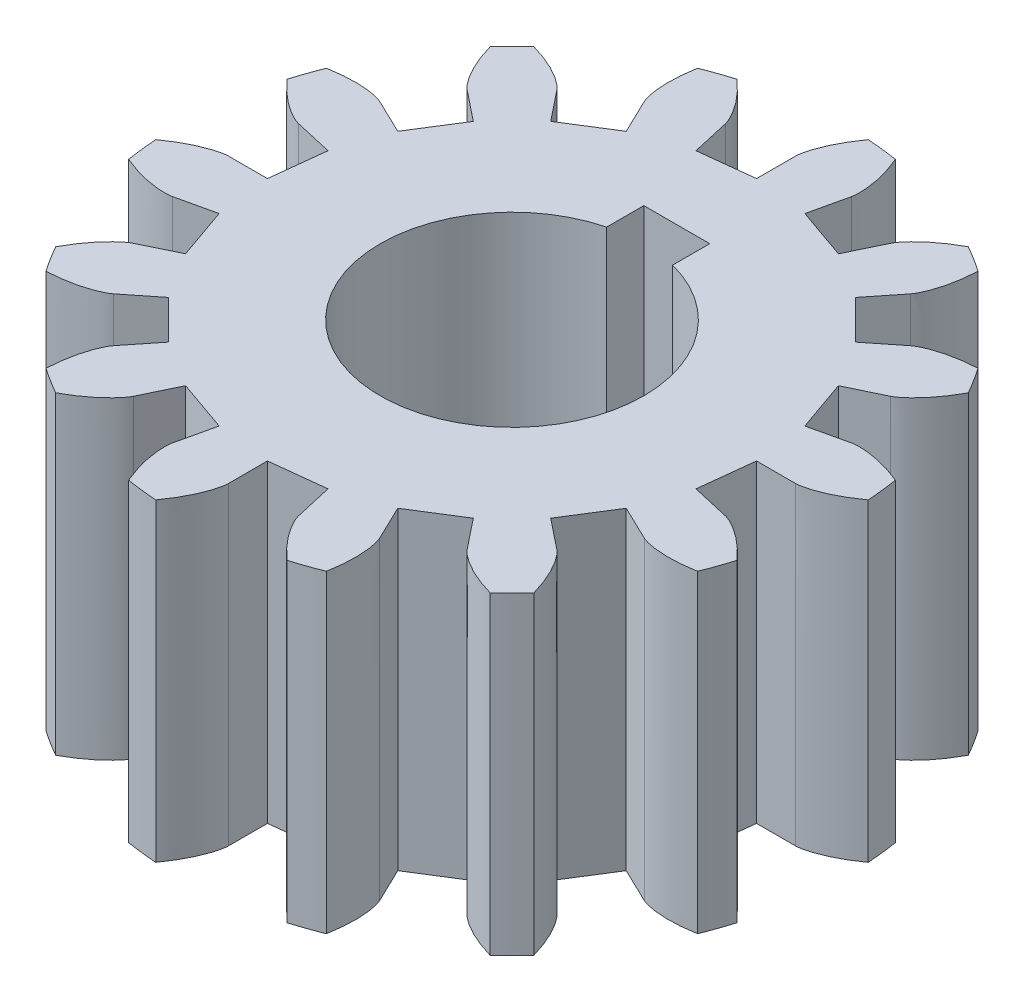
SolidWorks part; units mm, degrees
ref_plane "Front Plane" through (0, 0, 0) normal (0, 0, 1) x (1, 0, 0)
ref_plane "Top Plane" through (0, 0, 0) normal (0, 1, 0) x (1, 0, 0)
ref_plane "Right Plane" through (0, 0, 0) normal (1, 0, 0) x (0, 0, -1)
sketch "Sketch1" plane through (0, 0, 0) normal (0, 1, 0) x (1, 0, 0)
  line L0 (-8.6068, 0.0004) -> (-7.4206, 0.0003)
  line L1 (-7.7543, 3.7347) -> (-6.6856, 3.22)
  line L2 (-8.3911, -1.9148) -> (-7.2346, -1.6509)
  line L3 (-8.391, 1.9156) -> (-7.2345, 1.6515)
  line L4 (-5.366, 6.7293) -> (-4.6264, 5.8019)
  line L5 (-6.7289, 5.3666) -> (-5.8015, 4.6269)
  line L6 (-1.9148, 8.3911) -> (-1.6509, 7.2346)
  line L7 (-3.734, 7.7546) -> (-3.2194, 6.6859)
  line L8 (1.9156, 8.391) -> (1.6515, 7.2345)
  line L9 (0.0004, 8.6068) -> (0.0003, 7.4206)
  line L10 (5.3666, 6.7289) -> (4.6269, 5.8015)
  line L11 (3.7347, 7.7543) -> (3.22, 6.6856)
  line L12 (7.7546, 3.734) -> (6.6859, 3.2194)
  line L13 (6.7293, 5.366) -> (5.8019, 4.6264)
  line L14 (8.6068, -0.0004) -> (7.4206, -0.0003)
  line L15 (8.3911, 1.9148) -> (7.2346, 1.6509)
  line L16 (7.7543, -3.7347) -> (6.6856, -3.22)
  line L17 (8.391, -1.9156) -> (7.2345, -1.6515)
  line L18 (5.366, -6.7293) -> (4.6264, -5.8019)
  line L19 (6.7289, -5.3666) -> (5.8015, -4.6269)
  line L20 (1.9148, -8.3911) -> (1.6509, -7.2346)
  line L21 (3.734, -7.7546) -> (3.2194, -6.6859)
  line L22 (-1.9156, -8.391) -> (-1.6515, -7.2345)
  line L23 (-0.0004, -8.6068) -> (-0.0003, -7.4206)
  line L24 (-5.3666, -6.7289) -> (-4.6269, -5.8015)
  line L25 (-3.7347, -7.7543) -> (-3.22, -6.6856)
  line L26 (-7.7546, -3.734) -> (-6.6859, -3.2194)
  line L27 (-6.7293, -5.366) -> (-5.8019, -4.6264)
  line L28 (-7.2345, 1.6515) -> (-7.4206, 0.0003)
  line L29 (-5.8015, 4.6269) -> (-6.6856, 3.22)
  line L30 (-3.2194, 6.6859) -> (-4.6264, 5.8019)
  line L31 (0.0003, 7.4206) -> (-1.6509, 7.2346)
  line L33 (3.22, 6.6856) -> (1.6515, 7.2345)
  line L34 (5.8019, 4.6264) -> (4.6269, 5.8015)
  line L35 (7.2346, 1.6509) -> (6.6859, 3.2194)
  line L36 (7.2345, -1.6515) -> (7.4206, -0.0003)
  line L37 (5.8015, -4.6269) -> (6.6856, -3.22)
  line L38 (3.2194, -6.6859) -> (4.6264, -5.8019)
  line L39 (-0.0003, -7.4206) -> (1.6509, -7.2346)
  line L40 (-3.22, -6.6856) -> (-1.6515, -7.2345)
  line L41 (-5.8019, -4.6264) -> (-4.6269, -5.8015)
  line L42 (-7.2346, -1.6509) -> (-6.6859, -3.2194)
  line L44 (-1, 5) -> (1, 5)
  line L45 (-1, 5) -> (-1, 3.873)
  line L47 (1, 5) -> (1, 3.873)
  line L48 (1, 3) -> (1.008, 3.1002)
  arc A0 (-10.1378, -0.6707) -> (-10.033, -1.6011) centre (0, 0) ccw
  arc A1 (-9.4249, 3.7943) -> (-9.7342, 2.9106) centre (0, 0) ccw
  arc A2 (-6.8452, 7.5079) -> (-7.5073, 6.8459) centre (0, 0) ccw
  arc A3 (-2.9098, 9.7344) -> (-3.7935, 9.4252) centre (0, 0) ccw
  arc A4 (1.602, 10.0329) -> (0.6716, 10.1378) centre (0, 0) ccw
  arc A5 (5.7964, 8.3443) -> (5.0037, 8.8424) centre (0, 0) ccw
  arc A6 (8.8429, 5.0029) -> (8.3448, 5.7957) centre (0, 0) ccw
  arc A7 (10.1378, 0.6707) -> (10.033, 1.6011) centre (0, 0) ccw
  arc A8 (9.4249, -3.7943) -> (9.7342, -2.9106) centre (0, 0) ccw
  arc A9 (6.8452, -7.5079) -> (7.5073, -6.8459) centre (0, 0) ccw
  arc A10 (2.9098, -9.7344) -> (3.7935, -9.4252) centre (0, 0) ccw
  arc A11 (-1.602, -10.0329) -> (-0.6716, -10.1378) centre (0, 0) ccw
  arc A12 (-5.7964, -8.3443) -> (-5.0037, -8.8424) centre (0, 0) ccw
  arc A13 (-8.8429, -5.0029) -> (-8.3448, -5.7957) centre (0, 0) ccw
  arc A14 (-1, 3.873) -> (1, 3.873) centre (0, 0) ccw
  spline S0 degree 3 poles (-10.1378, -0.6707) (-10.0991, -0.6428) (-9.9923, -0.5669) (-9.8194, -0.4562) (-9.6238, -0.3435) (-9.442, -0.2507) (-9.2754, -0.1759) (-9.1252, -0.1174) (-8.9927, -0.0733) (-8.8788, -0.0417) (-8.7844, -0.0205) (-8.7103, -0.0081) (-8.6534, -0.0009) (-8.6212, 0) (-8.6068, 0.0004) knots 0.068878 0.068878 0.068878 0.068878 0.148295 0.284329 0.408535 0.520912 0.621459 0.710178 0.787068 0.852129 0.905361 0.946764 0.976338 1 1 1 1
  spline S1 degree 3 poles (-10.033, -1.6011) (-9.9891, -1.6198) (-9.8681, -1.6699) (-9.6748, -1.7394) (-9.4591, -1.8058) (-9.2612, -1.8558) (-9.0821, -1.8917) (-8.9227, -1.9153) (-8.7837, -1.9289) (-8.6656, -1.9343) (-8.5689, -1.934) (-8.4939, -1.9296) (-8.4368, -1.924) (-8.4052, -1.9177) (-8.3911, -1.9148) knots 0.068878 0.068878 0.068878 0.068878 0.148295 0.284329 0.408535 0.520912 0.621459 0.710178 0.787068 0.852129 0.905361 0.946764 0.976338 1 1 1 1
  spline S2 degree 3 poles (-9.4249, 3.7943) (-9.3779, 3.8027) (-9.2488, 3.8247) (-9.0449, 3.8494) (-8.8198, 3.8661) (-8.6157, 3.8708) (-8.4331, 3.8659) (-8.2725, 3.8535) (-8.1339, 3.8357) (-8.0176, 3.8148) (-7.9234, 3.7929) (-7.8512, 3.772) (-7.7968, 3.7538) (-7.7674, 3.7406) (-7.7543, 3.7347) knots 0.068878 0.068878 0.068878 0.068878 0.148295 0.284329 0.408535 0.520912 0.621459 0.710178 0.787068 0.852129 0.905361 0.946764 0.976338 1 1 1 1
  spline S3 degree 3 poles (-9.7342, 2.9106) (-9.7026, 2.8747) (-9.6154, 2.777) (-9.4714, 2.6306) (-9.3059, 2.4772) (-9.1493, 2.3462) (-9.0035, 2.2362) (-8.8701, 2.1458) (-8.7507, 2.0733) (-8.6467, 2.0171) (-8.5595, 1.9754) (-8.4899, 1.9468) (-8.4361, 1.9271) (-8.4048, 1.9191) (-8.391, 1.9156) knots 0.068878 0.068878 0.068878 0.068878 0.148295 0.284329 0.408535 0.520912 0.621459 0.710178 0.787068 0.852129 0.905361 0.946764 0.976338 1 1 1 1
  spline S4 degree 3 poles (-6.8452, 7.5079) (-6.7992, 7.4951) (-6.6734, 7.4588) (-6.4789, 7.3927) (-6.2689, 7.31) (-6.083, 7.2257) (-5.9206, 7.1421) (-5.7813, 7.0612) (-5.6641, 6.9851) (-5.5684, 6.9157) (-5.493, 6.8551) (-5.4371, 6.8049) (-5.396, 6.7649) (-5.3752, 6.7403) (-5.366, 6.7293) knots 0.068878 0.068878 0.068878 0.068878 0.148295 0.284329 0.408535 0.520912 0.621459 0.710178 0.787068 0.852129 0.905361 0.946764 0.976338 1 1 1 1
  spline S5 degree 3 poles (-7.5073, 6.8459) (-7.4945, 6.7999) (-7.4583, 6.674) (-7.3921, 6.4796) (-7.3095, 6.2695) (-7.2252, 6.0836) (-7.1416, 5.9212) (-7.0607, 5.7819) (-6.9846, 5.6647) (-6.9152, 5.569) (-6.8547, 5.4936) (-6.8045, 5.4377) (-6.7645, 5.3966) (-6.7398, 5.3758) (-6.7289, 5.3666) knots 0.068878 0.068878 0.068878 0.068878 0.148295 0.284329 0.408535 0.520912 0.621459 0.710178 0.787068 0.852129 0.905361 0.946764 0.976338 1 1 1 1
  spline S6 degree 3 poles (-2.9098, 9.7344) (-2.8739, 9.7029) (-2.7762, 9.6156) (-2.6298, 9.4717) (-2.4764, 9.3061) (-2.3455, 9.1495) (-2.2355, 9.0037) (-2.145, 8.8703) (-2.0725, 8.7509) (-2.0164, 8.6469) (-1.9747, 8.5596) (-1.9461, 8.4901) (-1.9264, 8.4362) (-1.9184, 8.405) (-1.9148, 8.3911) knots 0.068878 0.068878 0.068878 0.068878 0.148295 0.284329 0.408535 0.520912 0.621459 0.710178 0.787068 0.852129 0.905361 0.946764 0.976338 1 1 1 1
  spline S7 degree 3 poles (-3.7935, 9.4252) (-3.8019, 9.3782) (-3.8239, 9.2491) (-3.8487, 9.0452) (-3.8654, 8.8201) (-3.8701, 8.6161) (-3.8652, 8.4335) (-3.8528, 8.2728) (-3.8351, 8.1342) (-3.8141, 8.0179) (-3.7923, 7.9237) (-3.7713, 7.8515) (-3.7531, 7.7971) (-3.7399, 7.7677) (-3.734, 7.7546) knots 0.068878 0.068878 0.068878 0.068878 0.148295 0.284329 0.408535 0.520912 0.621459 0.710178 0.787068 0.852129 0.905361 0.946764 0.976338 1 1 1 1
  spline S8 degree 3 poles (1.602, 10.0329) (1.6206, 9.9889) (1.6708, 9.8679) (1.7403, 9.6747) (1.8066, 9.459) (1.8566, 9.2611) (1.8924, 9.082) (1.9161, 8.9225) (1.9296, 8.7835) (1.9351, 8.6655) (1.9347, 8.5688) (1.9303, 8.4937) (1.9247, 8.4366) (1.9184, 8.405) (1.9156, 8.391) knots 0.068878 0.068878 0.068878 0.068878 0.148295 0.284329 0.408535 0.520912 0.621459 0.710178 0.787068 0.852129 0.905361 0.946764 0.976338 1 1 1 1
  spline S9 degree 3 poles (0.6716, 10.1378) (0.6436, 10.0991) (0.5678, 9.9923) (0.457, 9.8193) (0.3443, 9.6238) (0.2515, 9.442) (0.1767, 9.2753) (0.1182, 9.1252) (0.0741, 8.9927) (0.0425, 8.8788) (0.0213, 8.7844) (0.0088, 8.7103) (0.0016, 8.6534) (0.0007, 8.6212) (0.0004, 8.6068) knots 0.068878 0.068878 0.068878 0.068878 0.148295 0.284329 0.408535 0.520912 0.621459 0.710178 0.787068 0.852129 0.905361 0.946764 0.976338 1 1 1 1
  spline S10 degree 3 poles (5.7964, 8.3443) (5.7942, 8.2966) (5.7869, 8.1658) (5.7656, 7.9615) (5.7318, 7.7384) (5.691, 7.5384) (5.6455, 7.3615) (5.5977, 7.2076) (5.5495, 7.0765) (5.5032, 6.9677) (5.461, 6.8807) (5.4245, 6.815) (5.3946, 6.766) (5.3752, 6.7403) (5.3666, 6.7289) knots 0.068878 0.068878 0.068878 0.068878 0.148295 0.284329 0.408535 0.520912 0.621459 0.710178 0.787068 0.852129 0.905361 0.946764 0.976338 1 1 1 1
  spline S11 degree 3 poles (5.0037, 8.8424) (4.9617, 8.8197) (4.847, 8.7564) (4.6722, 8.6486) (4.4858, 8.5213) (4.3233, 8.3978) (4.1836, 8.2801) (4.0657, 8.1702) (3.9685, 8.07) (3.8906, 7.9811) (3.8306, 7.9053) (3.7872, 7.8439) (3.756, 7.7957) (3.7413, 7.7671) (3.7347, 7.7543) knots 0.068878 0.068878 0.068878 0.068878 0.148295 0.284329 0.408535 0.520912 0.621459 0.710178 0.787068 0.852129 0.905361 0.946764 0.976338 1 1 1 1
  spline S12 degree 3 poles (8.8429, 5.0029) (8.8201, 4.9609) (8.7568, 4.8463) (8.649, 4.6715) (8.5217, 4.4851) (8.3982, 4.3226) (8.2805, 4.1829) (8.1706, 4.0651) (8.0703, 3.9678) (7.9814, 3.8899) (7.9056, 3.8299) (7.8442, 3.7865) (7.796, 3.7554) (7.7674, 3.7406) (7.7546, 3.734) knots 0.068878 0.068878 0.068878 0.068878 0.148295 0.284329 0.408535 0.520912 0.621459 0.710178 0.787068 0.852129 0.905361 0.946764 0.976338 1 1 1 1
  spline S13 degree 3 poles (8.3448, 5.7957) (8.297, 5.7935) (8.1663, 5.7862) (7.962, 5.7649) (7.7389, 5.7311) (7.5389, 5.6903) (7.3619, 5.6449) (7.208, 5.5971) (7.0769, 5.5489) (6.9682, 5.5026) (6.8812, 5.4604) (6.8155, 5.4239) (6.7665, 5.394) (6.7408, 5.3746) (6.7293, 5.366) knots 0.068878 0.068878 0.068878 0.068878 0.148295 0.284329 0.408535 0.520912 0.621459 0.710178 0.787068 0.852129 0.905361 0.946764 0.976338 1 1 1 1
  spline S14 degree 3 poles (10.1378, 0.6707) (10.0991, 0.6428) (9.9923, 0.5669) (9.8194, 0.4562) (9.6238, 0.3435) (9.442, 0.2507) (9.2754, 0.1759) (9.1252, 0.1174) (8.9927, 0.0733) (8.8788, 0.0417) (8.7844, 0.0205) (8.7103, 0.0081) (8.6534, 0.0009) (8.6212, 0) (8.6068, -0.0004) knots 0.068878 0.068878 0.068878 0.068878 0.148295 0.284329 0.408535 0.520912 0.621459 0.710178 0.787068 0.852129 0.905361 0.946764 0.976338 1 1 1 1
  spline S15 degree 3 poles (10.033, 1.6011) (9.9891, 1.6198) (9.8681, 1.6699) (9.6748, 1.7394) (9.4591, 1.8058) (9.2612, 1.8558) (9.0821, 1.8917) (8.9227, 1.9153) (8.7837, 1.9289) (8.6656, 1.9343) (8.5689, 1.934) (8.4939, 1.9296) (8.4368, 1.924) (8.4052, 1.9177) (8.3911, 1.9148) knots 0.068878 0.068878 0.068878 0.068878 0.148295 0.284329 0.408535 0.520912 0.621459 0.710178 0.787068 0.852129 0.905361 0.946764 0.976338 1 1 1 1
  spline S16 degree 3 poles (9.4249, -3.7943) (9.3779, -3.8027) (9.2488, -3.8247) (9.0449, -3.8494) (8.8198, -3.8661) (8.6157, -3.8708) (8.4331, -3.8659) (8.2725, -3.8535) (8.1339, -3.8357) (8.0176, -3.8148) (7.9234, -3.7929) (7.8512, -3.772) (7.7968, -3.7538) (7.7674, -3.7406) (7.7543, -3.7347) knots 0.068878 0.068878 0.068878 0.068878 0.148295 0.284329 0.408535 0.520912 0.621459 0.710178 0.787068 0.852129 0.905361 0.946764 0.976338 1 1 1 1
  spline S17 degree 3 poles (9.7342, -2.9106) (9.7026, -2.8747) (9.6154, -2.777) (9.4714, -2.6306) (9.3059, -2.4772) (9.1493, -2.3462) (9.0035, -2.2362) (8.8701, -2.1458) (8.7507, -2.0733) (8.6467, -2.0171) (8.5595, -1.9754) (8.4899, -1.9468) (8.4361, -1.9271) (8.4048, -1.9191) (8.391, -1.9156) knots 0.068878 0.068878 0.068878 0.068878 0.148295 0.284329 0.408535 0.520912 0.621459 0.710178 0.787068 0.852129 0.905361 0.946764 0.976338 1 1 1 1
  spline S18 degree 3 poles (6.8452, -7.5079) (6.7992, -7.4951) (6.6734, -7.4588) (6.4789, -7.3927) (6.2689, -7.31) (6.083, -7.2257) (5.9206, -7.1421) (5.7813, -7.0612) (5.6641, -6.9851) (5.5684, -6.9157) (5.493, -6.8551) (5.4371, -6.8049) (5.396, -6.7649) (5.3752, -6.7403) (5.366, -6.7293) knots 0.068878 0.068878 0.068878 0.068878 0.148295 0.284329 0.408535 0.520912 0.621459 0.710178 0.787068 0.852129 0.905361 0.946764 0.976338 1 1 1 1
  spline S19 degree 3 poles (7.5073, -6.8459) (7.4945, -6.7999) (7.4583, -6.674) (7.3921, -6.4796) (7.3095, -6.2695) (7.2252, -6.0836) (7.1416, -5.9212) (7.0607, -5.7819) (6.9846, -5.6647) (6.9152, -5.569) (6.8547, -5.4936) (6.8045, -5.4377) (6.7645, -5.3966) (6.7398, -5.3758) (6.7289, -5.3666) knots 0.068878 0.068878 0.068878 0.068878 0.148295 0.284329 0.408535 0.520912 0.621459 0.710178 0.787068 0.852129 0.905361 0.946764 0.976338 1 1 1 1
  spline S20 degree 3 poles (2.9098, -9.7344) (2.8739, -9.7029) (2.7762, -9.6156) (2.6298, -9.4717) (2.4764, -9.3061) (2.3455, -9.1495) (2.2355, -9.0037) (2.145, -8.8703) (2.0725, -8.7509) (2.0164, -8.6469) (1.9747, -8.5596) (1.9461, -8.4901) (1.9264, -8.4362) (1.9184, -8.405) (1.9148, -8.3911) knots 0.068878 0.068878 0.068878 0.068878 0.148295 0.284329 0.408535 0.520912 0.621459 0.710178 0.787068 0.852129 0.905361 0.946764 0.976338 1 1 1 1
  spline S21 degree 3 poles (3.7935, -9.4252) (3.8019, -9.3782) (3.8239, -9.2491) (3.8487, -9.0452) (3.8654, -8.8201) (3.8701, -8.6161) (3.8652, -8.4335) (3.8528, -8.2728) (3.8351, -8.1342) (3.8141, -8.0179) (3.7923, -7.9237) (3.7713, -7.8515) (3.7531, -7.7971) (3.7399, -7.7677) (3.734, -7.7546) knots 0.068878 0.068878 0.068878 0.068878 0.148295 0.284329 0.408535 0.520912 0.621459 0.710178 0.787068 0.852129 0.905361 0.946764 0.976338 1 1 1 1
  spline S22 degree 3 poles (-1.602, -10.0329) (-1.6206, -9.9889) (-1.6708, -9.8679) (-1.7403, -9.6747) (-1.8066, -9.459) (-1.8566, -9.2611) (-1.8924, -9.082) (-1.9161, -8.9225) (-1.9296, -8.7835) (-1.9351, -8.6655) (-1.9347, -8.5688) (-1.9303, -8.4937) (-1.9247, -8.4366) (-1.9184, -8.405) (-1.9156, -8.391) knots 0.068878 0.068878 0.068878 0.068878 0.148295 0.284329 0.408535 0.520912 0.621459 0.710178 0.787068 0.852129 0.905361 0.946764 0.976338 1 1 1 1
  spline S23 degree 3 poles (-0.6716, -10.1378) (-0.6436, -10.0991) (-0.5678, -9.9923) (-0.457, -9.8193) (-0.3443, -9.6238) (-0.2515, -9.442) (-0.1767, -9.2753) (-0.1182, -9.1252) (-0.0741, -8.9927) (-0.0425, -8.8788) (-0.0213, -8.7844) (-0.0088, -8.7103) (-0.0016, -8.6534) (-0.0007, -8.6212) (-0.0004, -8.6068) knots 0.068878 0.068878 0.068878 0.068878 0.148295 0.284329 0.408535 0.520912 0.621459 0.710178 0.787068 0.852129 0.905361 0.946764 0.976338 1 1 1 1
  spline S24 degree 3 poles (-5.7964, -8.3443) (-5.7942, -8.2966) (-5.7869, -8.1658) (-5.7656, -7.9615) (-5.7318, -7.7384) (-5.691, -7.5384) (-5.6455, -7.3615) (-5.5977, -7.2076) (-5.5495, -7.0765) (-5.5032, -6.9677) (-5.461, -6.8807) (-5.4245, -6.815) (-5.3946, -6.766) (-5.3752, -6.7403) (-5.3666, -6.7289) knots 0.068878 0.068878 0.068878 0.068878 0.148295 0.284329 0.408535 0.520912 0.621459 0.710178 0.787068 0.852129 0.905361 0.946764 0.976338 1 1 1 1
  spline S25 degree 3 poles (-5.0037, -8.8424) (-4.9617, -8.8197) (-4.847, -8.7564) (-4.6722, -8.6486) (-4.4858, -8.5213) (-4.3233, -8.3978) (-4.1836, -8.2801) (-4.0657, -8.1702) (-3.9685, -8.07) (-3.8906, -7.9811) (-3.8306, -7.9053) (-3.7872, -7.8439) (-3.756, -7.7957) (-3.7413, -7.7671) (-3.7347, -7.7543) knots 0.068878 0.068878 0.068878 0.068878 0.148295 0.284329 0.408535 0.520912 0.621459 0.710178 0.787068 0.852129 0.905361 0.946764 0.976338 1 1 1 1
  spline S26 degree 3 poles (-8.8429, -5.0029) (-8.8201, -4.9609) (-8.7568, -4.8463) (-8.649, -4.6715) (-8.5217, -4.4851) (-8.3982, -4.3226) (-8.2805, -4.1829) (-8.1706, -4.0651) (-8.0703, -3.9678) (-7.9814, -3.8899) (-7.9056, -3.8299) (-7.8442, -3.7865) (-7.796, -3.7554) (-7.7674, -3.7406) (-7.7546, -3.734) knots 0.068878 0.068878 0.068878 0.068878 0.148295 0.284329 0.408535 0.520912 0.621459 0.710178 0.787068 0.852129 0.905361 0.946764 0.976338 1 1 1 1
  spline S27 degree 3 poles (-8.3448, -5.7957) (-8.297, -5.7935) (-8.1663, -5.7862) (-7.962, -5.7649) (-7.7389, -5.7311) (-7.5389, -5.6903) (-7.3619, -5.6449) (-7.208, -5.5971) (-7.0769, -5.5489) (-6.9682, -5.5026) (-6.8812, -5.4604) (-6.8155, -5.4239) (-6.7665, -5.394) (-6.7408, -5.3746) (-6.7293, -5.366) knots 0.068878 0.068878 0.068878 0.068878 0.148295 0.284329 0.408535 0.520912 0.621459 0.710178 0.787068 0.852129 0.905361 0.946764 0.976338 1 1 1 1
  point P414 (0, 4)
  dimension "D1" = 8
extrude "Extrude1" add sketch "Sketch1" along normal blind 9.525 contours A13 S27 L27 L41 L24 S24 A12 S25 L25 L40 L22 S22 A11 S23 L23 L39 L20 S20 A10 S21 L21 L38 L18 S18 A9 S19 L19 L37 L16 S16 A8 S17 L17 L36 L14 S14 A7 S15 L15 L35 L12 S12 A6 S13 L13 L34 L10 S10 A5 S11 L11
